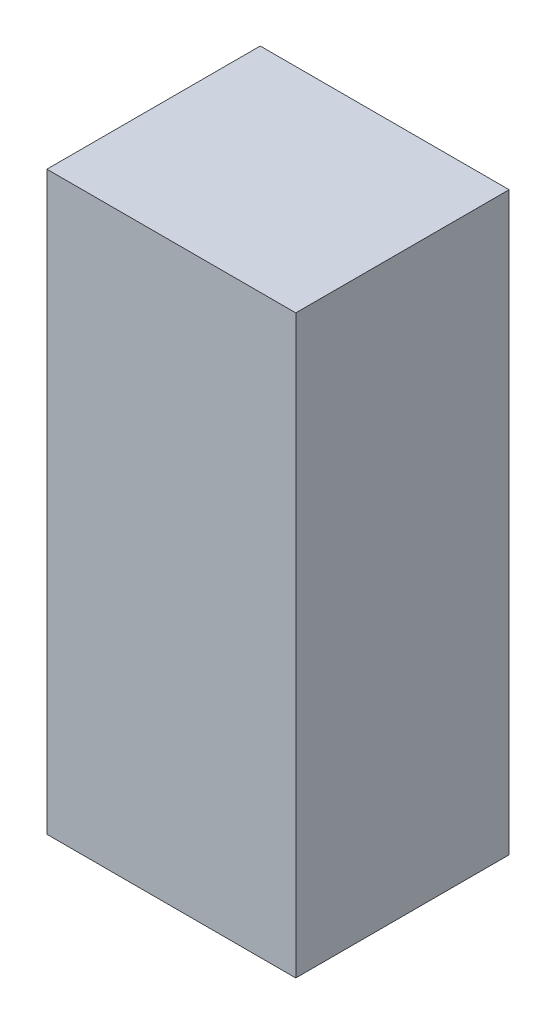
SolidWorks part; units mm, degrees
ref_plane "Front Plane" through (0, 0, 0) normal (0, 0, 1) x (1, 0, 0)
ref_plane "Top Plane" through (0, 0, 0) normal (0, 1, 0) x (1, 0, 0)
ref_plane "Right Plane" through (0, 0, 0) normal (1, 0, 0) x (0, 0, -1)
sketch "Sketch1" plane through (0, 0, 0) normal (0, 1, 0) x (1, 0, 0)
  line L1 (0, 0) -> (175, 0)
  line L2 (0, 0) -> (0, 150)
  line L3 (0, 150) -> (175, 150)
  line L4 (175, 0) -> (175, 150)
  dimension "D1" = 175
  dimension "D2" = 150
extrude "Boss-Extrude1" add sketch "Sketch1" along normal blind 405
